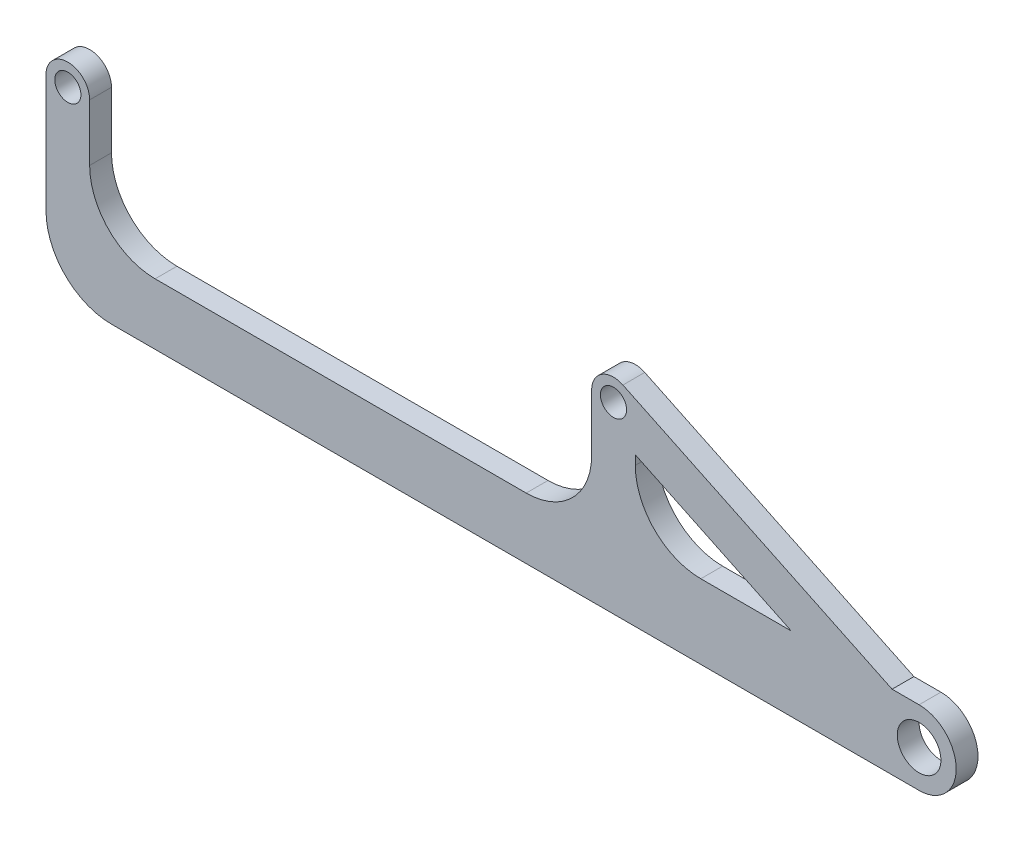
SolidWorks part; units mm, degrees
ref_plane "Front Plane" through (0, 0, 0) normal (0, 0, 1) x (1, 0, 0)
ref_plane "Top Plane" through (0, 0, 0) normal (0, 1, 0) x (1, 0, 0)
ref_plane "Right Plane" through (0, 0, 0) normal (1, 0, 0) x (0, 0, -1)
sketch "Sketch1" plane through (0, 0, 0) normal (0, 0, 1) x (1, 0, 0)
  line L0 (0, 0) -> (125, 0) construction
  line L1 (125, 0) -> (273, 0)
  line L3 (0, 0) -> (-5, 0) construction
  line L4 (5, 0) -> (5, -28)
  line L5 (5, -28) -> (39.1198, -28)
  line L6 (-5, 0) -> (-5, -42)
  line L7 (-5, -42) -> (2, -42)
  line L8 (125, 0) -> (125, 5)
  line L9 (120, 0) -> (120, -28)
  line L10 (120, -28) -> (39.1198, -28)
  line L12 (130, -42) -> (2, -42)
  line L13 (130, 0) -> (130, -25)
  line L14 (130, -25) -> (195, -25)
  line L16 (195, -42) -> (130, -42)
  line L17 (125, 0) -> (195, -33.5)
  line L18 (195, -33.5) -> (197.808, -25.4772)
  line L20 (195, -33.5) -> (192.6133, -37.8936)
  line L22 (124.0047, -2.8301) -> (126.6518, 4.7193)
  line L23 (125, 0) -> (127.1584, 4.5101)
  line L24 (127.1584, 4.5101) -> (197.1584, -28.9899)
  line L25 (125, 0) -> (123.7049, -2.7061)
  line L26 (195, -33.5) -> (193.3482, -38.2193)
  line L27 (193.3482, -38.2193) -> (130, -7.9026)
  circle A0 centre (0, 0) radius 3
  circle A1 centre (125, 0) radius 3
  circle A6 centre (20, -13) radius 15
  circle A7 centre (195, -33.5) radius 5
  arc A8 (-5, 0) -> (5, 0) centre (0, 0) cw
  arc A9 (120, 0) -> (130, 0) centre (125, 0) cw
  arc A10 (195, -25) -> (195, -42) centre (195, -33.5) cw
  circle A11 centre (105, -13) radius 15
  circle A12 centre (145, -10) radius 15
  circle A13 centre (10, -27) radius 15
  dimension "D1" = 14
  dimension "D3" = 5
  dimension "D7" = 65
  dimension "D2" = 42
  dimension "D4" = 5
  dimension "D5" = 5
  dimension "D6" = 5
  dimension "D8" = 125
  dimension "D9" = 8.5
  dimension "D10" = 8.5
extrude "Boss-Extrude1" add sketch "Sketch1" along normal blind 5 contours A13 L12 L16 A10 L18 L24 A7 L27 L14 L13 L17 A1 L8 A9 L9 L10 L5 | A10 L14 L24 L18 | A7 L18 L24 L14 L17 | A7 L17 L14 L27 | A12 L17 L14 L24 | A12 L27 L14 L17 | L17 A12 L27 | L1 A12 L17 L24 | A12 L17 L13 L27 | A12 L1 L13 L17 | A12 L24 A9 L1 | L24 A12 L1 | A9 L23 A1 L1 | A1 L17 L13 L1 | A9 L8 A1 L22 | A9 L22 A1 L23 | A12 L13 L14 | A11 L10 L9 | A6 L4 L5 | L4 A13 L5 | A13 L4 A8 L6 A0
